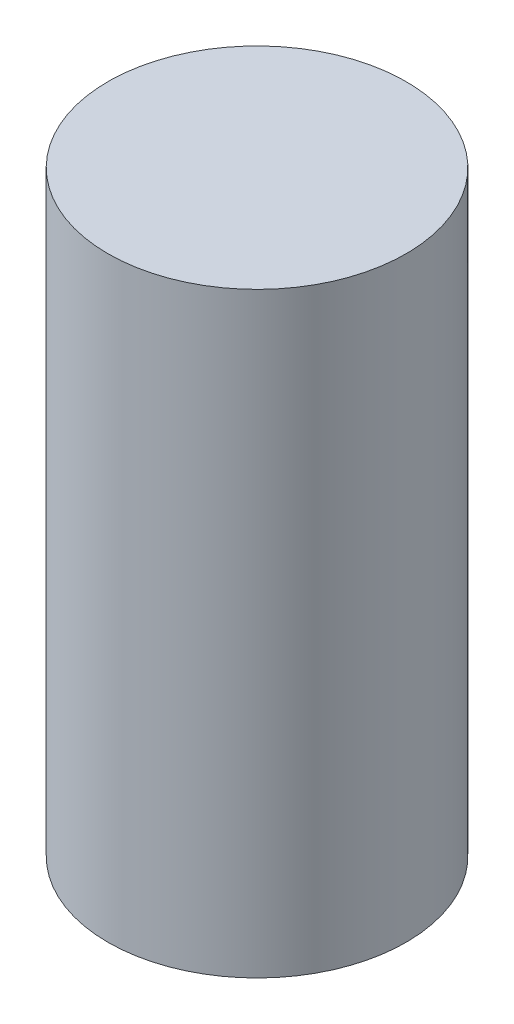
SolidWorks part; units mm, degrees
ref_plane "Ebene vorne" through (0, 0, 0) normal (0, 0, 1) x (1, 0, 0)
ref_plane "Ebene oben" through (0, 0, 0) normal (0, 1, 0) x (1, 0, 0)
ref_plane "Ebene rechts" through (0, 0, 0) normal (1, 0, 0) x (0, 0, -1)
sketch "Skizze1" plane through (0, 0, 0) normal (0, 1, 0) x (1, 0, 0)
  circle A0 centre (0, 0) radius 50
  dimension "D1" = 100
extrude "Aufsatz-Linear austragen1" add sketch "Skizze1" along normal blind 200 contours A0
